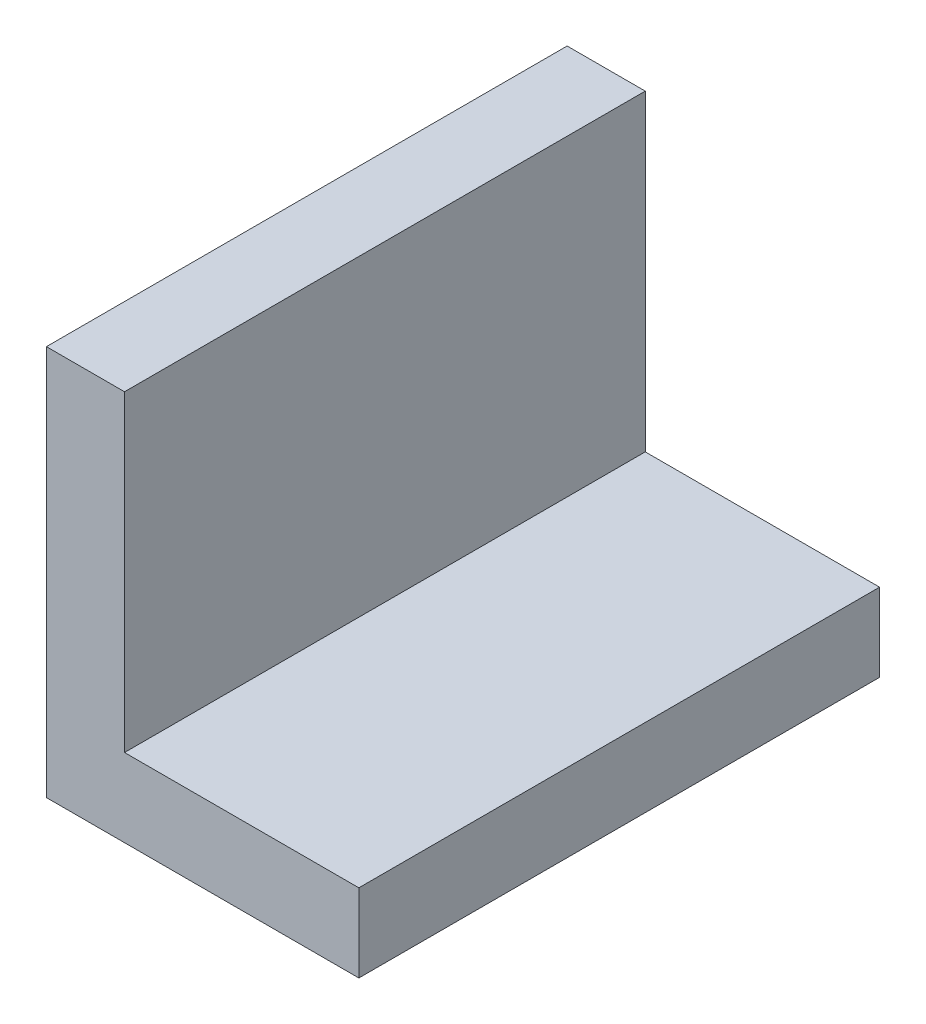
SolidWorks part; units mm, degrees
ref_plane "Front Plane" through (0, 0, 0) normal (0, 0, 1) x (1, 0, 0)
ref_plane "Top Plane" through (0, 0, 0) normal (0, 1, 0) x (1, 0, 0)
ref_plane "Right Plane" through (0, 0, 0) normal (1, 0, 0) x (0, 0, -1)
sketch "Sketch1" plane through (0, 0, 0) normal (0, 0, 1) x (1, 0, 0)
  line L0 (0, 0) -> (60, 0)
  line L1 (60, 0) -> (60, 15)
  line L2 (60, 15) -> (15, 15)
  line L3 (15, 15) -> (15, 75)
  line L4 (15, 75) -> (0, 75)
  line L5 (0, 75) -> (0, 0)
  dimension "D1" = 75
  dimension "D2" = 60
  dimension "D3" = 15
  dimension "D4" = 15
extrude "Boss-Extrude1" add sketch "Sketch1" along normal blind 100
